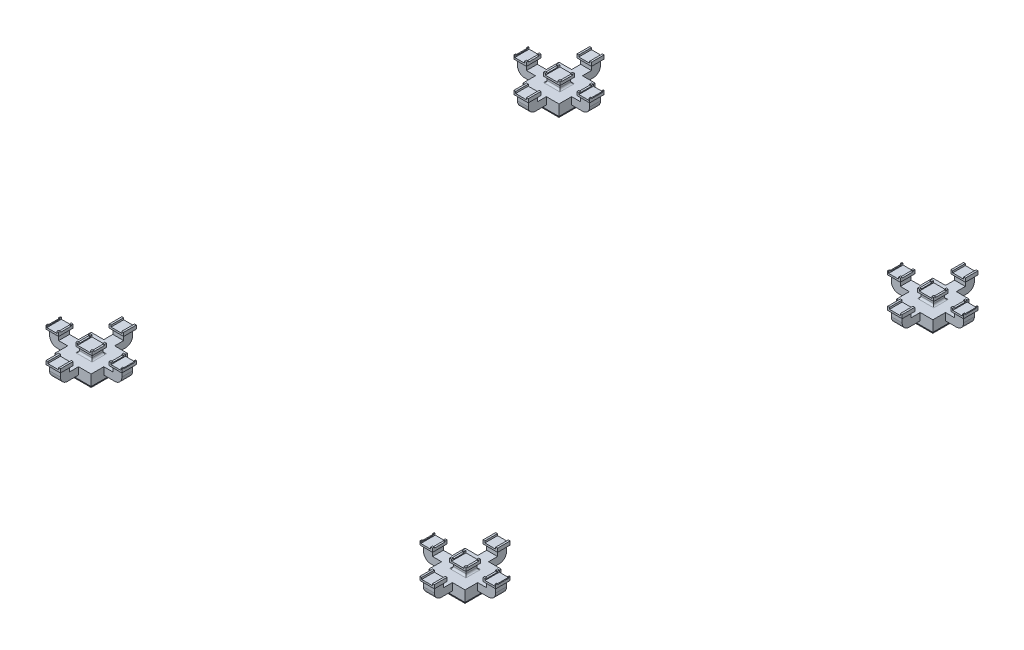
SolidWorks part; units mm, degrees
material "松木"
ref_plane "前视基准面" through (0, 0, 0) normal (0, 0, 1) x (1, 0, 0)
ref_plane "上视基准面" through (0, 0, 0) normal (0, 1, 0) x (1, 0, 0)
ref_plane "右视基准面" through (0, 0, 0) normal (1, 0, 0) x (0, 0, -1)
sketch "草图1" plane through (0, 0, 0) normal (0, 1, 0) x (1, 0, 0)
  line L1 (0, 0) -> (50, 0)
  line L2 (0, 0) -> (0, 50)
  line L3 (0, 50) -> (50, 50)
  line L4 (50, 0) -> (50, 50)
  dimension "D1" = 50
  dimension "D2" = 50
extrude "凸台-拉伸1" add sketch "草图1" along normal blind 70
sketch "草图2" plane through (0, 70, 0) normal (0, 1, 0) x (1, 0, 0)
  line L0 (-50, -50) -> (-50, 100)
  line L1 (0, 0) -> (50, 0)
  line L2 (0, 0) -> (0, 50)
  line L3 (0, 50) -> (50, 50)
  line L4 (50, 0) -> (50, 50)
  line L5 (-50, 100) -> (100, 100)
  line L6 (100, -50) -> (100, 100)
  line L7 (-50, -50) -> (100, -50)
  dimension "D1" = 50
ref_plane "基准面4" through (0, 70, 0) normal (0, 1, 0) x (1, 0, 0)
ref_plane "基准面5" through (0, 100, 0) normal (0, 1, 0) x (1, 0, 0)
sketch "草图3" plane through (0, 100, 0) normal (0, 1, 0) x (1, 0, 0)
  line L0 (-75, -75) -> (-75, 125)
  line L1 (-50, -50) -> (100, -50)
  line L2 (-50, -50) -> (-50, 100)
  line L3 (-50, 100) -> (100, 100)
  line L4 (100, -50) -> (100, 100)
  line L5 (-75, 125) -> (125, 125)
  line L6 (125, -75) -> (125, 125)
  line L7 (-75, -75) -> (125, -75)
  dimension "D1" = 25
loft "放样2" add section "草图2" section "草图3"
sketch "草图4" plane through (0, 100, 0) normal (0, 1, 0) x (1, 0, 0)
  line L1 (125, -75) -> (-75, -75)
  line L2 (125, -75) -> (125, 125)
  line L3 (125, 125) -> (-75, 125)
  line L4 (-75, -75) -> (-75, 125)
extrude "凸台-拉伸2" add sketch "草图4" along normal blind 20
sketch "草图5" plane through (0, 120, 0) normal (0, 1, 0) x (1, 0, 0)
  line L1 (-75, -75) -> (-5, -75)
  line L2 (-75, -75) -> (-75, -5)
  line L3 (-75, -5) -> (-5, -5)
  line L4 (-5, -75) -> (-5, -5)
  line L5 (125, -75) -> (55, -75)
  line L6 (125, -75) -> (125, -5)
  line L7 (125, -5) -> (55, -5)
  line L8 (55, -75) -> (55, -5)
  line L9 (125, 125) -> (55, 125)
  line L10 (125, 125) -> (125, 55)
  line L11 (125, 55) -> (55, 55)
  line L12 (55, 125) -> (55, 55)
  line L13 (-75, 125) -> (-5, 125)
  line L14 (-75, 125) -> (-75, 55)
  line L15 (-75, 55) -> (-5, 55)
  line L16 (-5, 125) -> (-5, 55)
  dimension "D1" = 70
  dimension "D2" = 70
extrude "凸台-拉伸3" add sketch "草图5" along normal blind 40
sketch "草图6" plane through (0, 120, 0) normal (0, 1, 0) x (1, 0, 0)
  line L0 (-75, 55) -> (-5, 55) construction
  line L1 (-175, -5) -> (225, -5)
  line L2 (-175, -5) -> (-175, 55)
  line L3 (-175, 55) -> (225, 55)
  line L4 (225, -5) -> (225, 55)
  line L5 (-5, -5) -> (-75, -5) construction
  line L7 (55, 125) -> (-5, 125) construction
  point P10 (25, 55)
  point P13 (25, 125)
  dimension "D1" = 400
extrude "凸台-拉伸4" add sketch "草图6" along normal blind 40
sketch "草图7" plane through (0, 160, 0) normal (0, 1, 0) x (1, 0, 0)
  line L0 (225, 55) -> (125, 55) construction
  line L1 (225, -5) -> (175, -5)
  line L2 (225, -5) -> (225, 55)
  line L3 (225, 55) -> (175, 55)
  line L4 (175, -5) -> (175, 55)
  line L5 (-75, 55) -> (-175, 55) construction
  line L6 (-175, -5) -> (-125, -5)
  line L7 (-175, -5) -> (-175, 55)
  line L8 (-175, 55) -> (-125, 55)
  line L9 (-125, -5) -> (-125, 55)
  line L10 (125, 55) -> (125, 125) construction
  line L11 (55, -5) -> (125, -5)
  line L12 (55, -5) -> (55, 55)
  line L13 (55, 55) -> (125, 55)
  line L14 (125, -5) -> (125, 55)
  line L16 (-5, -5) -> (-75, -5)
  line L17 (-5, -5) -> (-5, 55)
  line L18 (-5, 55) -> (-75, 55)
  line L19 (-75, -5) -> (-75, 55)
extrude "凸台-拉伸6" add sketch "草图7" along normal blind 20
sketch "草图8" plane through (0, 180, 0) normal (0, 1, 0) x (1, 0, 0)
  line L0 (-75, -5) -> (-5, -5) construction
  line L1 (-75, 55) -> (-10, 55)
  line L2 (-75, 55) -> (-75, -5)
  line L3 (-75, -5) -> (-10, -5)
  line L4 (-10, 55) -> (-10, -5)
  line L5 (55, -5) -> (125, -5) construction
  line L6 (125, 55) -> (60, 55)
  line L7 (125, 55) -> (125, -5)
  line L8 (125, -5) -> (60, -5)
  line L9 (60, 55) -> (60, -5)
  line L10 (-5, -5) -> (-5, 55) construction
  line L11 (55, 55) -> (55, -5) construction
  dimension "D1" = 5
  dimension "D2" = 5
extrude "切除-拉伸1" cut sketch "草图8" against normal blind 20
fillet "圆角1" radius 40 2 edges at (-175, 120, -25) (225, 120, -25)
ref_plane "基准面6" through (0, 180, 0) normal (0, 1, 0) x (1, 0, 0)
ref_plane "基准面7" through (0, 190, 0) normal (0, 1, 0) x (1, 0, 0)
sketch "草图9" plane through (0, 190, 0) normal (0, 1, 0) x (1, 0, 0)
  line L0 (235, 65) -> (235, -15)
  line L1 (225, 55) -> (175, 55)
  line L2 (225, 55) -> (225, -5)
  line L3 (225, -5) -> (175, -5)
  line L4 (175, 55) -> (175, -5)
  line L5 (-175, 55) -> (-125, 55)
  line L6 (-175, 55) -> (-175, -5)
  line L7 (-175, -5) -> (-125, -5)
  line L8 (-125, 55) -> (-125, -5)
  line L9 (235, -15) -> (165, -15)
  line L10 (165, 65) -> (165, -15)
  line L11 (235, 65) -> (165, 65)
  line L12 (-185, 65) -> (-185, -15)
  line L13 (-185, -15) -> (-115, -15)
  line L14 (-115, 65) -> (-115, -15)
  line L15 (-185, 65) -> (-115, 65)
  dimension "D1" = 10
  dimension "D2" = 10
sketch "草图10" plane through (0, 180, 0) normal (0, 1, 0) x (1, 0, 0)
  line L1 (225, 55) -> (175, 55)
  line L2 (225, 55) -> (225, -5)
  line L3 (225, -5) -> (175, -5)
  line L4 (175, 55) -> (175, -5)
  line L5 (-125, 55) -> (-175, 55)
  line L6 (-125, 55) -> (-125, -5)
  line L7 (-125, -5) -> (-175, -5)
  line L8 (-175, 55) -> (-175, -5)
loft "放样3" add section "草图10" section "草图9"
ref_plane "基准面8" through (25, 0, 0) normal (1, 0, 0) x (0, 0, -1)
sketch "草图12" plane through (0, 190, 0) normal (0, 1, 0) x (1, 0, 0)
  line L1 (165, -15) -> (235, -15)
  line L2 (165, -15) -> (165, 65)
  line L3 (165, 65) -> (235, 65)
  line L4 (235, -15) -> (235, 65)
extrude "凸台-拉伸7" add sketch "草图12" along normal blind 10
sketch "草图13" plane through (0, 200, 0) normal (0, 1, 0) x (1, 0, 0)
  line L0 (235, 65) -> (165, 65) construction
  line L1 (165, -15) -> (175, -15)
  line L2 (165, -15) -> (165, 65)
  line L3 (165, 65) -> (175, 65)
  line L4 (175, -15) -> (175, 65)
  line L6 (235, -15) -> (230, -15)
  line L7 (235, -15) -> (235, 65)
  line L8 (235, 65) -> (230, 65)
  line L9 (230, -15) -> (230, 65)
  dimension "D1" = 10
  dimension "D2" = 5
extrude "凸台-拉伸8" add sketch "草图13" along normal blind 10
mirror "镜向2" about plane through (25, 0, 0) normal (1, 0, 0) of "放样3", "凸台-拉伸7", "凸台-拉伸8"
sketch "草图15" plane through (0, 120, 0) normal (0, 1, 0) x (1, 0, 0)
  line L0 (55, 125) -> (55, 55) construction
  line L1 (55, 225) -> (-5, 225)
  line L2 (55, 225) -> (55, -175)
  line L3 (55, -175) -> (-5, -175)
  line L4 (-5, 225) -> (-5, -175)
  line L5 (-5, 55) -> (-5, 125) construction
  line L6 (-5, -5) -> (-5, 55) construction
  point P8 (-5, 25)
  point P11 (-5, 25)
  dimension "D1" = 400
extrude "凸台-拉伸9" add sketch "草图15" along normal blind 40
sketch "草图16" plane through (0, 160, 0) normal (0, 1, 0) x (1, 0, 0)
  line L0 (-5, -75) -> (-5, -175) construction
  line L1 (55, -175) -> (-5, -175)
  line L2 (55, -175) -> (55, -125)
  line L3 (55, -125) -> (-5, -125)
  line L4 (-5, -175) -> (-5, -125)
  line L5 (55, 125) -> (55, 225) construction
  line L6 (-5, 225) -> (55, 225)
  line L7 (-5, 225) -> (-5, 175)
  line L8 (-5, 175) -> (55, 175)
  line L9 (55, 225) -> (55, 175)
extrude "凸台-拉伸10" add sketch "草图16" along normal blind 20
sketch "草图17" plane through (0, 180, 0) normal (0, 1, 0) x (1, 0, 0)
  line L1 (55, -175) -> (-5, -175)
  line L2 (55, -175) -> (55, -125)
  line L3 (55, -125) -> (-5, -125)
  line L4 (-5, -175) -> (-5, -125)
  line L5 (55, 225) -> (-5, 225)
  line L6 (55, 225) -> (55, 175)
  line L7 (55, 175) -> (-5, 175)
  line L8 (-5, 225) -> (-5, 175)
sketch "草图18" plane through (0, 190, 0) normal (0, 1, 0) x (1, 0, 0)
  line L0 (65, -185) -> (65, -115)
  line L1 (55, -175) -> (-5, -175)
  line L2 (55, -175) -> (55, -125)
  line L3 (55, -125) -> (-5, -125)
  line L4 (-5, -175) -> (-5, -125)
  line L9 (65, -115) -> (-15, -115)
  line L10 (-15, -185) -> (-15, -115)
  line L11 (65, -185) -> (-15, -185)
  dimension "D1" = 10
loft "放样4" add section "草图18" section "草图17"
ref_plane "基准面10" through (0, 0, -25) normal (0, 0, 1) x (1, 0, 0)
sketch "草图19" plane through (0, 190, 0) normal (0, 1, 0) x (1, 0, 0)
  line L12 (-15, -185) -> (65, -185)
  line L13 (-15, -185) -> (-15, -115)
  line L14 (-15, -115) -> (65, -115)
  line L15 (65, -185) -> (65, -115)
extrude "凸台-拉伸12" add sketch "草图19" along normal blind 10
sketch "草图20" plane through (0, 200, 0) normal (0, 1, 0) x (1, 0, 0)
  line L0 (-15, -185) -> (65, -185) construction
  line L1 (-15, -115) -> (-5, -115)
  line L2 (-15, -115) -> (-15, -185)
  line L3 (-15, -185) -> (-5, -185)
  line L4 (-5, -115) -> (-5, -185)
  line L6 (65, -115) -> (55, -115)
  line L7 (65, -115) -> (65, -185)
  line L8 (65, -185) -> (55, -185)
  line L9 (55, -115) -> (55, -185)
  dimension "D1" = 10
  dimension "D2" = 10
extrude "凸台-拉伸13" add sketch "草图20" along normal blind 10
mirror "镜向3" about plane through (0, 0, -25) normal (0, 0, 1) of "放样4", "凸台-拉伸12", "凸台-拉伸13"
fillet "圆角3" radius 10 2 edges at (60, 160, -25) (-10, 160, -25)
sketch "草图21" plane through (0, 160, 0) normal (0, 1, 0) x (1, 0, 0)
  line L1 (-5, -5) -> (55, -5)
  line L2 (-5, -5) -> (-5, 55)
  line L3 (-5, 55) -> (55, 55)
  line L4 (55, -5) -> (55, 55)
extrude "凸台-拉伸14" add sketch "草图21" along normal blind 20
fillet "圆角4" radius 10 2 edges at (25, 160, -55) (25, 160, 5)
sketch "草图22" plane through (0, 180, 0) normal (0, 1, 0) x (1, 0, 0)
  line L1 (-10, -5) -> (60, -5)
  line L2 (-10, -5) -> (-10, 55)
  line L3 (-10, 55) -> (60, 55)
  line L4 (60, -5) -> (60, 55)
sketch "草图23" plane through (0, 190, 0) normal (0, 1, 0) x (1, 0, 0)
  line L0 (-20, -15) -> (-20, 65)
  line L1 (-10, -5) -> (60, -5)
  line L2 (-10, -5) -> (-10, 55)
  line L3 (-10, 55) -> (60, 55)
  line L4 (60, -5) -> (60, 55)
  line L5 (-20, 65) -> (70, 65)
  line L6 (70, -15) -> (70, 65)
  line L7 (-20, -15) -> (70, -15)
  dimension "D1" = 10
loft "放样5" add profiles "草图22" section "草图22" section "草图23"
sketch "草图24" plane through (0, 190, 0) normal (0, 1, 0) x (1, 0, 0)
  line L0 (-20, 65) -> (70, 65) construction
  line L1 (-20, -15) -> (-10, -15)
  line L2 (-20, -15) -> (-20, 65)
  line L3 (-20, 65) -> (-10, 65)
  line L5 (-20, -15) -> (70, -15) construction
  line L6 (70, 65) -> (60, 65)
  line L7 (70, 65) -> (70, -15)
  line L8 (70, -15) -> (60, -15)
  line L11 (-20, -15) -> (70, -15)
  line L12 (-20, -15) -> (-20, 65)
  line L13 (-20, 65) -> (70, 65)
  line L14 (70, -15) -> (70, 65)
  dimension "D1" = 10
  dimension "D2" = 10
extrude "凸台-拉伸15" add sketch "草图24" along normal blind 10
sketch "草图25" plane through (0, 200, 0) normal (0, 1, 0) x (1, 0, 0)
  line L0 (70, 65) -> (-20, 65) construction
  line L1 (-20, -15) -> (-10, -15)
  line L2 (-20, -15) -> (-20, 65)
  line L3 (-20, 65) -> (-10, 65)
  line L4 (-10, -15) -> (-10, 65)
  line L5 (-20, -15) -> (70, -15) construction
  line L6 (70, 65) -> (60, 65)
  line L7 (70, 65) -> (70, -15)
  line L8 (70, -15) -> (60, -15)
  line L9 (60, 65) -> (60, -15)
  dimension "D1" = 10
  dimension "D2" = 10
extrude "凸台-拉伸16" add sketch "草图25" along normal blind 10
sketch "草图26" plane through (0, 210, 0) normal (0, 1, 0) x (1, 0, 0)
  line L0 (230, -15) -> (235, -15) construction
  line L1 (235, -5) -> (-185, -5)
  line L2 (235, -5) -> (235, 55)
  line L3 (235, 55) -> (-185, 55)
  line L4 (-185, -5) -> (-185, 55)
  line L5 (235, 65) -> (230, 65) construction
  line L6 (-185, -15) -> (-185, 65) construction
  line L7 (235, -15) -> (235, 65) construction
  dimension "D1" = 10
  dimension "D2" = 10
extrude "切除-拉伸2" cut sketch "草图26" against normal blind 5
fillet "圆角5" radius 40 2 edges at (25, 120, -225) (25, 120, 175)
scale "缩放比例1" scale about origin uniform scaling yes scale factor 2
sketch "草图30" plane through (0, 0, 0) normal (0, -1, 0) x (1, 0, 0)
  line L1 (100, 0) -> (0, 0)
  line L2 (100, 0) -> (100, -100)
  line L3 (100, -100) -> (0, -100)
  line L4 (0, 0) -> (0, -100)
  line L8 (90, -10) -> (90, -90)
  line L9 (90, -90) -> (10, -90)
  line L10 (10, -10) -> (10, -90)
  line L11 (90, -10) -> (10, -10)
  dimension "D1" = 10
extrude "切除-拉伸4" cut sketch "草图30" against normal blind 140
sketch "草图31" plane through (10, 0, 0) normal (-1, 0, 0) x (0, 0, 1)
  line L0 (-10, 140) -> (-10, 0) construction
  line L1 (-90, 0) -> (-10, 0)
  line L2 (-90, 0) -> (-90, 40)
  line L3 (-90, 40) -> (-10, 40)
  line L4 (-10, 0) -> (-10, 40)
  dimension "D1" = 40
extrude "切除-拉伸5" cut sketch "草图31" against normal blind 140
pattern_linear "阵列(线性)1" count 2 spacing 5180 along (0, 0, -1) count 2 spacing 4140 along (1, 0, 0) of bodies 136
